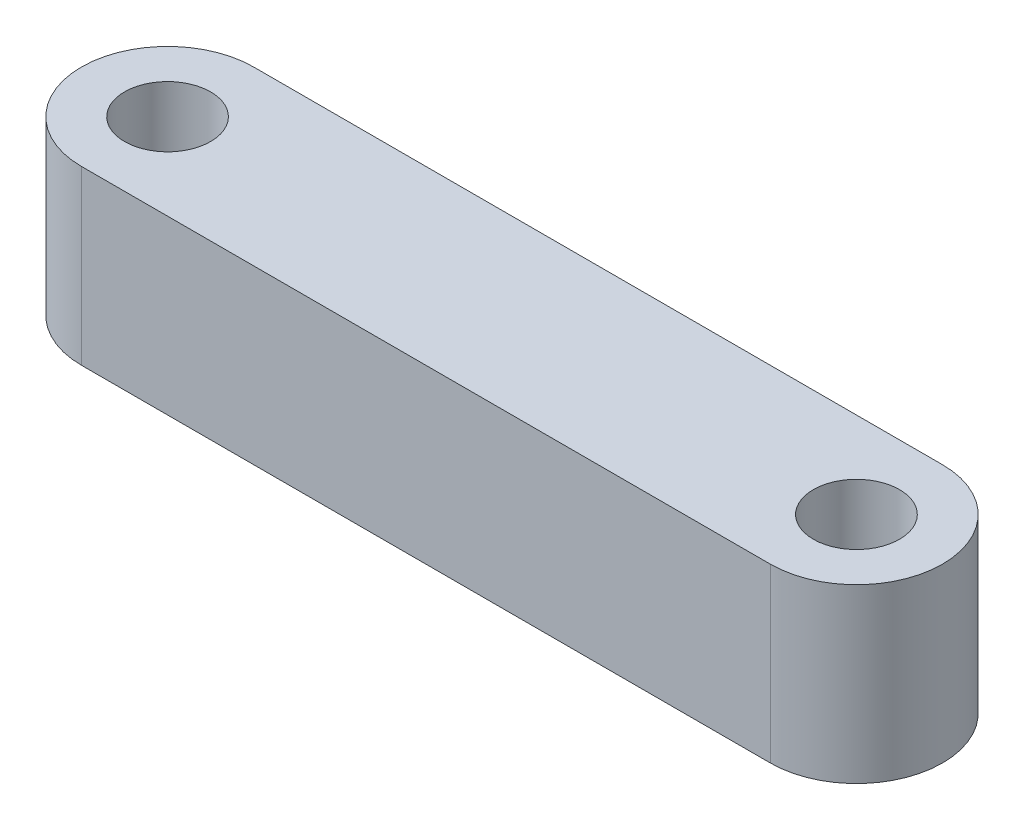
SolidWorks part; units mm, degrees
ref_plane "Front Plane" through (0, 0, 0) normal (0, 0, 1) x (1, 0, 0)
ref_plane "Top Plane" through (0, 0, 0) normal (0, 1, 0) x (1, 0, 0)
ref_plane "Right Plane" through (0, 0, 0) normal (1, 0, 0) x (0, 0, -1)
sketch "Sketch3" plane through (0, 0, 0) normal (0, 1, 0) x (1, 0, 0)
  line L0 (0, 15) -> (120, 15)
  line L1 (0, -15) -> (120, -15)
  arc A0 (0, 15) -> (0, -15) centre (0, 0) ccw
  arc A1 (0, 15) -> (0, -15) centre (0, 0) ccw
  circle A2 centre (0, 0) radius 7.5
  circle A3 centre (120, 0) radius 7.5
  arc A4 (120, 15) -> (120, -15) centre (120, 0) cw
  dimension "D3" = 120
  dimension "D4" = 30
extrude "Boss-Extrude1" add sketch "Sketch3" along normal blind 30 contours A4 L0 A0 L1 A2 A3
